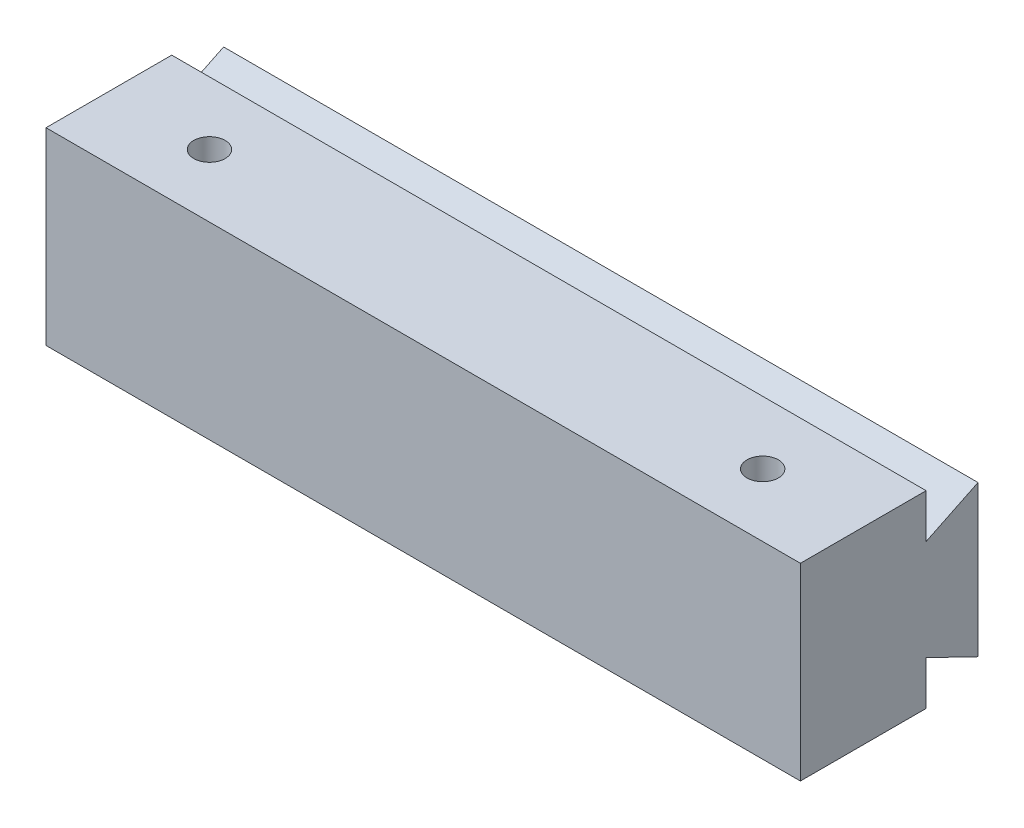
SolidWorks part; units mm, degrees
ref_plane "Front Plane" through (0, 0, 0) normal (0, 0, 1) x (1, 0, 0)
ref_plane "Top Plane" through (0, 0, 0) normal (0, 1, 0) x (1, 0, 0)
ref_plane "Right Plane" through (0, 0, 0) normal (1, 0, 0) x (0, 0, -1)
sketch "Sketch1" plane through (0, 0, 0) normal (0, 0, 1) x (1, 0, 0)
  line L1 (-30, -7.5) -> (30, -7.5)
  line L2 (-30, -7.5) -> (-30, 7.5)
  line L3 (-30, 7.5) -> (30, 7.5)
  line L4 (30, -7.5) -> (30, 7.5)
  line L5 (-30, -7.5) -> (30, 7.5) construction
  line L6 (-30, 7.5) -> (30, -7.5) construction
  point P0 (0, 0)
  dimension "D1" = 15
  dimension "D2" = 60
extrude "Boss-Extrude1" add sketch "Sketch1" along normal blind 10
sketch "Sketch2" plane through (30, 0, 0) normal (1, 0, 0) x (0, 0, -1)
  line L0 (0, 4) -> (4.1248, 6)
  line L1 (0, -7.5) -> (0, 7.5) construction
  line L2 (4.1248, 6) -> (4.1248, -6)
  line L3 (4.1248, -6) -> (0, -4)
  line L4 (0, 4) -> (0, -4)
  dimension "D1" = 4
  dimension "D2" = 4
  dimension "D3" = 2
  dimension "D4" = 2
extrude "Boss-Extrude2" add sketch "Sketch2" against normal up to surface (60 mm away) up to face at (-30, 0, 5)
sketch "Sketch3" plane through (0, 7.5, 0) normal (0, 1, 0) x (1, 0, 0)
  line L0 (-30, -10) -> (-30, 0) construction
  line L1 (30, -10) -> (30, 0) construction
  circle A0 centre (-22, -5) radius 1.25
  circle A1 centre (22, -5) radius 1.25
  dimension "D1" = 2.5
  dimension "D2" = 2.5
  dimension "D3" = 8
  dimension "D4" = 8
extrude "Cut-Extrude1" cut sketch "Sketch3" against normal through all both and the other way through all
